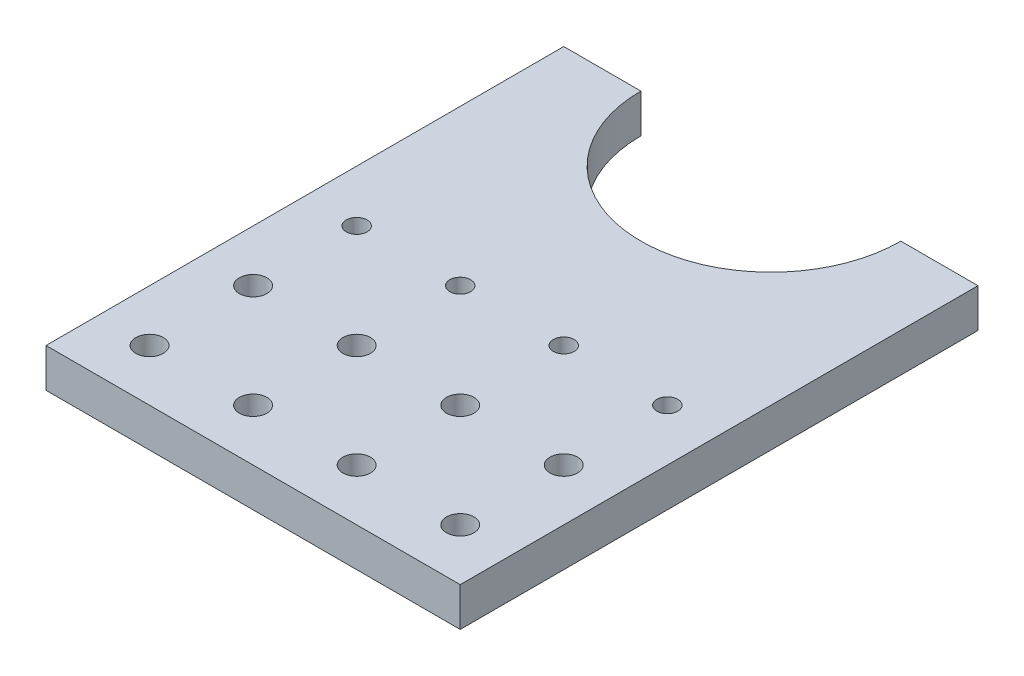
SolidWorks part; units mm, degrees
ref_plane "Front Plane" through (0, 0, 0) normal (0, 0, 1) x (1, 0, 0)
ref_plane "Top Plane" through (0, 0, 0) normal (0, 1, 0) x (1, 0, 0)
ref_plane "Right Plane" through (0, 0, 0) normal (1, 0, 0) x (0, 0, -1)
sketch "Sketch1" plane through (0, 0, 0) normal (0, 1, 0) x (1, 0, 0)
  line L1 (0, 0) -> (101.6, 0)
  line L2 (0, 0) -> (0, 127)
  line L3 (0, 127) -> (101.6, 127)
  line L4 (101.6, 0) -> (101.6, 127)
extrude "Boss-Extrude1" add sketch "Sketch1" along normal blind 9.525
sketch "Sketch2" plane through (0, 9.525, 0) normal (0, 1, 0) x (1, 0, 0)
  line L0 (101.6, 127) -> (0, 127) construction
  circle A0 centre (50.8, 127) radius 31.877
extrude "Cut-Extrude1" cut sketch "Sketch2" against normal through all
hole_wizard "1/4 Clearance Hole1" positions "Sketch4" profile "Sketch3" hole size "1/4" standard "Ansi Inch" end condition through all
sketch "Sketch4" plane through (0, 9.525, 0) normal (0, 1, 0) x (-1, 0, 0)
  point P0 (-12.7, -12.7)
sketch "Sketch3" plane through (12.7, 9.525, -12.7) normal (1, 0, 0) x (0, 0, 1)
  line L0 (0, 0) -> (0, 9.525)
  line L1 (0, 9.525) -> (3.3782, 9.525)
  line L2 (3.3782, 9.525) -> (3.3782, 0)
  line L5 (3.3782, 0) -> (0, 0)
  line L11 (0, -6.35) -> (0, 107.95) construction
  dimension "Thru Hole Dia." = 6.7564
  dimension "Thru Hole Depth" = 9.525
pattern_linear "LPattern1" count 2 spacing 25.4 along (0, 0, -1) count 4 spacing 25.4 along (1, 0, 0) of "1/4 Clearance Hole1"
hole_wizard "Tap Drill for 1/4-20 Tap1" positions "Sketch6" profile "Sketch5" hole size "1/4-20" standard "Ansi Inch" end condition through all
sketch "Sketch6" plane through (0, 9.525, 0) normal (0, 1, 0) x (-1, 0, 0)
  point P0 (-12.7, -63.5)
sketch "Sketch5" plane through (12.7, 9.525, -63.5) normal (1, 0, 0) x (0, 0, 1)
  line L0 (0, 0) -> (0, 9.525)
  line L1 (0, 9.525) -> (2.5527, 9.525)
  line L2 (2.5527, 9.525) -> (2.5527, 0)
  line L5 (2.5527, 0) -> (0, 0)
  line L11 (0, -6.35) -> (0, 107.95) construction
  dimension "Thru Hole Dia." = 5.1054
  dimension "Thru Hole Depth" = 9.525
pattern_linear "LPattern2" count 4 spacing 25.4 along (1, 0, 0) of "Tap Drill for 1/4-20 Tap1"
